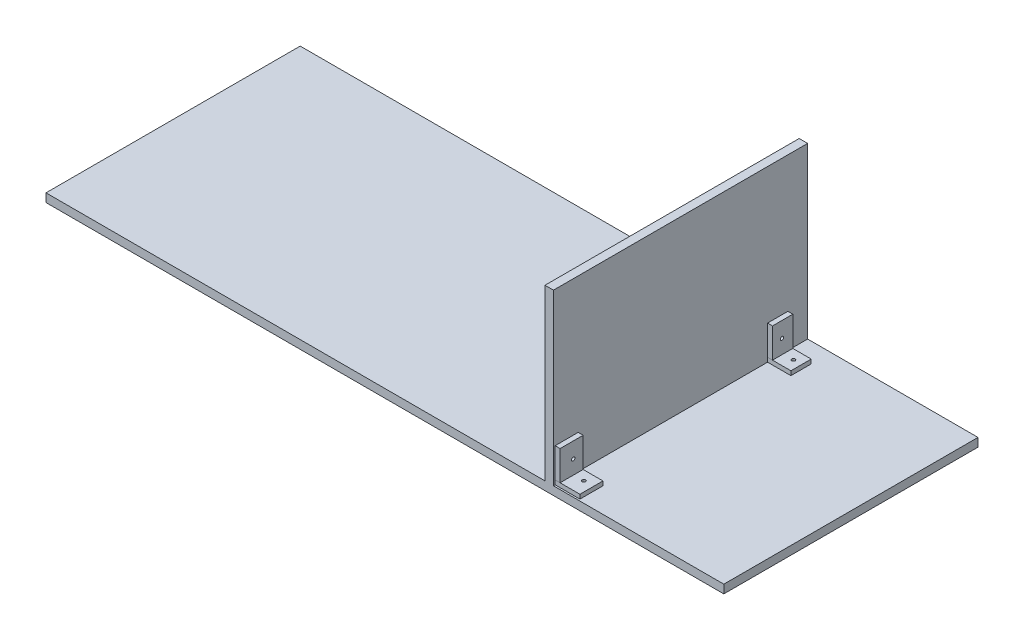
SolidWorks part; units mm, degrees
ref_plane "Front Plane" through (0, 0, 0) normal (0, 0, 1) x (1, 0, 0)
ref_plane "Top Plane" through (0, 0, 0) normal (0, 1, 0) x (1, 0, 0)
ref_plane "Right Plane" through (0, 0, 0) normal (1, 0, 0) x (0, 0, -1)
sketch "Sketch1" plane through (0, 0, 0) normal (0, 1, 0) x (1, 0, 0)
  line L1 (-635.5134, 161.5909) -> (164.4866, 161.5909)
  line L2 (-635.5134, 161.5909) -> (-635.5134, -138.4091)
  line L3 (-635.5134, -138.4091) -> (164.4866, -138.4091)
  line L4 (164.4866, 161.5909) -> (164.4866, -138.4091)
  dimension "D1" = 800
  dimension "D2" = 300
extrude "Boss-Extrude1" add sketch "Sketch1" along normal blind 10
sketch "Sketch2" plane through (0, 10, 0) normal (0, 1, 0) x (1, 0, 0)
  line L0 (164.4866, 161.5909) -> (-635.5134, 161.5909) construction
  line L1 (-46.5676, 161.5909) -> (-36.5676, 161.5909)
  line L2 (-46.5676, 161.5909) -> (-46.5676, -138.4091)
  line L3 (-46.5676, -138.4091) -> (-36.5676, -138.4091)
  line L4 (-36.5676, 161.5909) -> (-36.5676, -138.4091)
  line L5 (-635.5134, -138.4091) -> (164.4866, -138.4091) construction
  dimension "D1" = 10
extrude "Boss-Extrude2" add sketch "Sketch2" along normal blind 200
sketch "Sketch4" plane through (0, 10, 0) normal (0, 1, 0) x (1, 0, 0)
  line L1 (-36.5676, -109.2286) -> (-7.3436, -109.2286)
  line L2 (-36.5676, -109.2286) -> (-36.5676, -136.4154)
  line L3 (-36.5676, -136.4154) -> (-7.3436, -136.4154)
  line L4 (-7.3436, -109.2286) -> (-7.3436, -136.4154)
  line L5 (-36.5676, -138.4091) -> (-36.5676, 161.5909) construction
  line L6 (-9.0341, 114.2797) -> (-36.5676, 114.2797)
  line L7 (-9.0341, 114.2797) -> (-9.0341, 138.2236)
  line L8 (-9.0341, 138.2236) -> (-36.5676, 138.2236)
  line L9 (-36.5676, 114.2797) -> (-36.5676, 138.2236)
extrude "Boss-Extrude4" add sketch "Sketch4" along normal blind 5 separate body
sketch "Sketch5" plane through (0, 15, 0) normal (0, 1, 0) x (1, 0, 0)
  line L0 (-7.3436, -109.2286) -> (-36.5676, -109.2286) construction
  line L1 (-36.5676, -136.4154) -> (-30.7388, -136.4154)
  line L2 (-36.5676, -136.4154) -> (-36.5676, -109.2286)
  line L3 (-36.5676, -109.2286) -> (-30.7388, -109.2286)
  line L4 (-30.7388, -136.4154) -> (-30.7388, -109.2286)
  line L5 (-9.0341, 138.2236) -> (-36.5676, 138.2236) construction
  line L6 (-36.5676, 114.2797) -> (-30.7388, 114.2797)
  line L7 (-36.5676, 114.2797) -> (-36.5676, 138.2236)
  line L8 (-36.5676, 138.2236) -> (-30.7388, 138.2236)
  line L9 (-30.7388, 114.2797) -> (-30.7388, 138.2236)
extrude "Boss-Extrude5" add sketch "Sketch5" along normal blind 35 separate body
hole_wizard "Ø4.0mm Dowel Hole1" positions "Sketch8" profile "Sketch7" hole size "Ø4.0" standard "ANSI Metric" end condition through all
sketch "Sketch8" plane through (0, 15, 0) normal (0, 1, 0) x (1, 0, 0)
  point P0 (-18.688, -120.3587)
  point P2 (-18.688, 126.9158)
sketch "Sketch7" plane through (-18.688, 15, 120.3587) normal (1, 0, 0) x (0, 0, 1)
  line L0 (0, 0) -> (0, 15)
  line L1 (0, 15) -> (2, 15)
  line L2 (2, 15) -> (2, 0)
  line L5 (2, 0) -> (0, 0)
  line L11 (0, -6.35) -> (0, 107.95) construction
  dimension "Thru Hole Dia." = 4
  dimension "Thru Hole Depth" = 15
hole_wizard "Ø4.0mm Dowel Hole2" positions "Sketch10" profile "Sketch9" hole size "Ø4.0" standard "ANSI Metric" end condition through all
sketch "Sketch10" plane through (-30.7388, 0, 0) normal (1, 0, 0) x (0, 0, -1)
  point P0 (-120.9177, 31.6173)
  point P2 (125.4755, 31.6173)
sketch "Sketch9" plane through (-30.7388, 31.6173, 120.9177) normal (0, 1, 0) x (0, 0, -1)
  line L0 (0, 0) -> (0, 604.7746)
  line L1 (0, 604.7746) -> (2, 604.7746)
  line L2 (2, 604.7746) -> (2, 0)
  line L5 (2, 0) -> (0, 0)
  line L11 (0, -6.35) -> (0, 107.95) construction
  dimension "Thru Hole Dia." = 4
  dimension "Thru Hole Depth" = 604.7746
